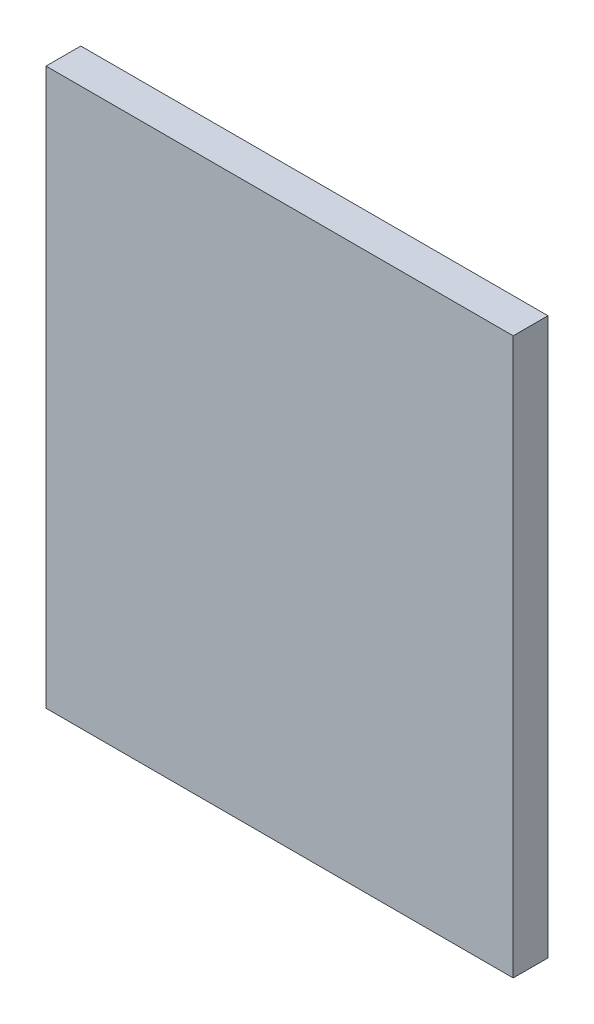
SolidWorks part; units mm, degrees
ref_plane "Front Plane" through (0, 0, 0) normal (0, 0, 1) x (1, 0, 0)
ref_plane "Top Plane" through (0, 0, 0) normal (0, 1, 0) x (1, 0, 0)
ref_plane "Right Plane" through (0, 0, 0) normal (1, 0, 0) x (0, 0, -1)
sketch "Sketch2" plane through (0, 0, 0) normal (0, 0, 1) x (1, 0, 0)
  line L1 (-21.336, -25.4) -> (21.336, -25.4)
  line L2 (-21.336, -25.4) -> (-21.336, 25.4)
  line L3 (-21.336, 25.4) -> (21.336, 25.4)
  line L4 (21.336, -25.4) -> (21.336, 25.4)
  line L5 (-21.336, -25.4) -> (21.336, 25.4) construction
  line L6 (-21.336, 25.4) -> (21.336, -25.4) construction
  point P0 (0, 0)
  dimension "D1" = 42.672
  dimension "D2" = 50.8
extrude "Boss-Extrude1" add sketch "Sketch2" along normal mid plane 3.175
